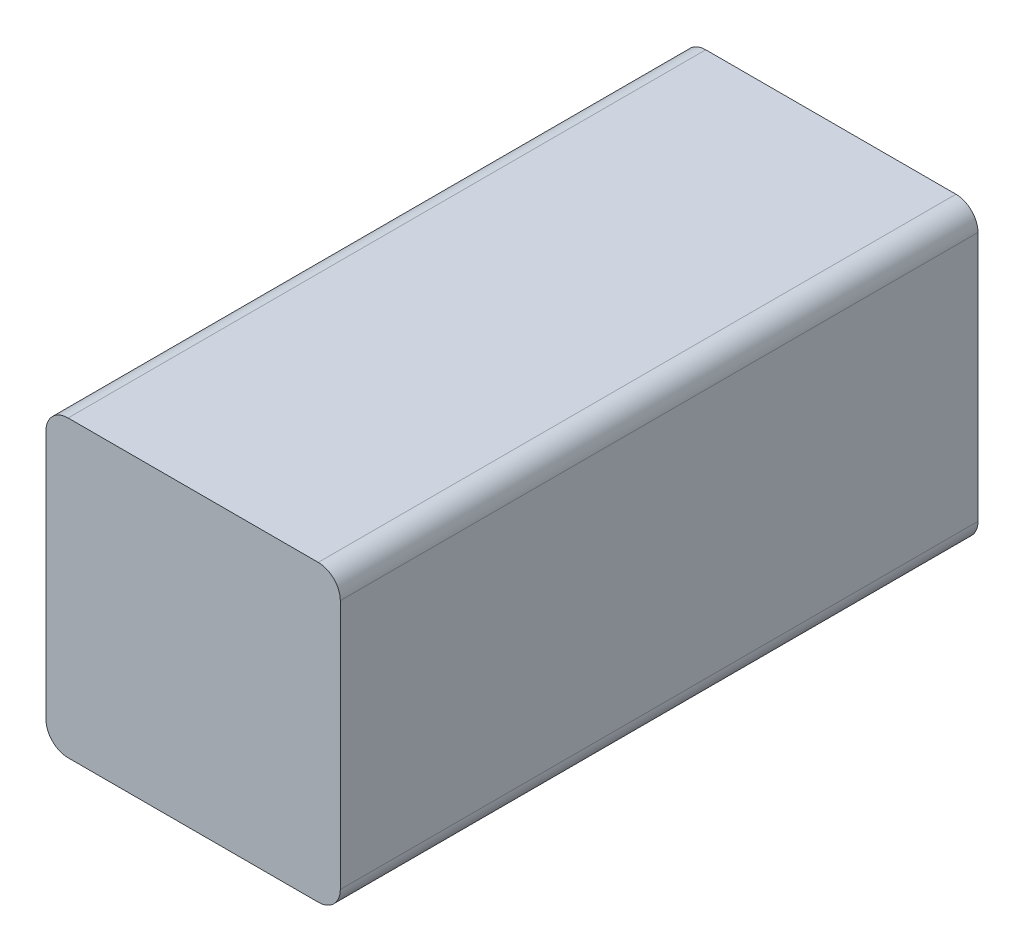
SolidWorks part; units mm, degrees
ref_plane "Plan de face" through (0, 0, 0) normal (0, 0, 1) x (1, 0, 0)
ref_plane "Plan de dessus" through (0, 0, 0) normal (0, 1, 0) x (1, 0, 0)
ref_plane "Plan de droite" through (0, 0, 0) normal (1, 0, 0) x (0, 0, -1)
sketch "Esquisse1" plane through (0, 0, 0) normal (0, 0, 1) x (1, 0, 0)
  line L0 (0, -63.3691) -> (0, 71.2902) construction
  line L1 (-75.6108, 0) -> (80.6515, 0) construction
  line L2 (-15, 12.75) -> (-15, -12.75)
  line L3 (-12.75, 15) -> (12.75, 15)
  line L4 (-12.75, -15) -> (12.75, -15)
  line L6 (15, 12.75) -> (15, -12.75)
  arc A0 (12.75, 15) -> (15, 12.75) centre (12.75, 12.75) cw
  arc A1 (-12.75, 15) -> (-15, 12.75) centre (-12.75, 12.75) ccw
  arc A2 (-12.75, -15) -> (-15, -12.75) centre (-12.75, -12.75) cw
  arc A3 (12.75, -15) -> (15, -12.75) centre (12.75, -12.75) ccw
  point P5 (-15, 0)
  point P14 (0, 15)
  point P20 (0, -15)
  point P21 (15, 0)
  dimension "D3" = 2.25
  dimension "D1" = 30
  dimension "D2" = 30
extrude "Extrusion1" add sketch "Esquisse1" along normal blind 65
